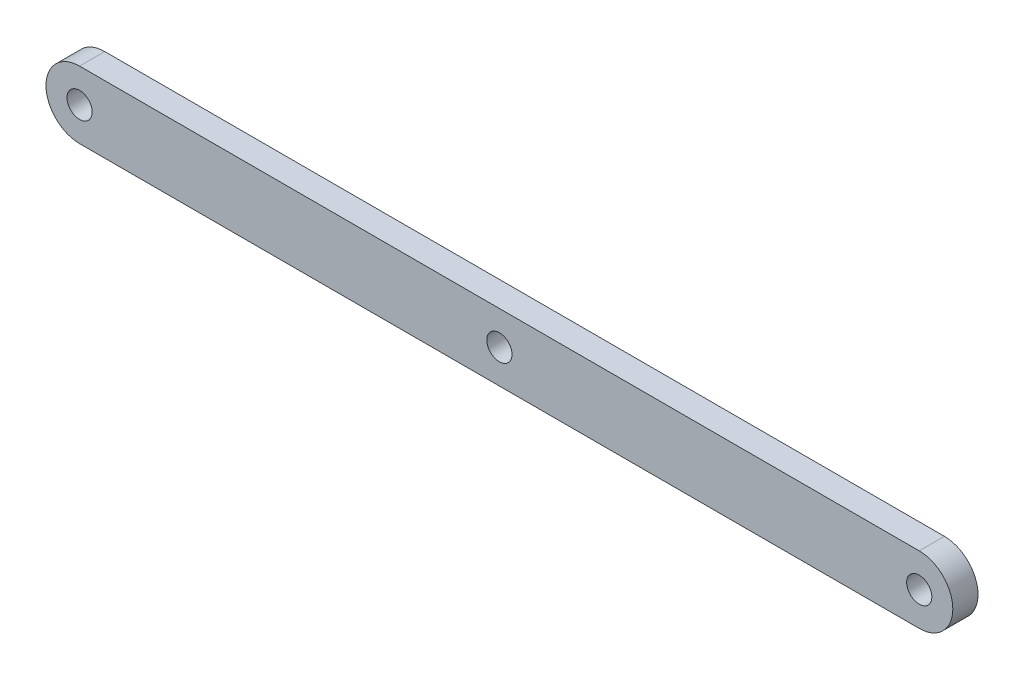
SolidWorks part; units mm, degrees
ref_plane "Front Plane" through (0, 0, 0) normal (0, 0, 1) x (1, 0, 0)
ref_plane "Top Plane" through (0, 0, 0) normal (0, 1, 0) x (1, 0, 0)
ref_plane "Right Plane" through (0, 0, 0) normal (1, 0, 0) x (0, 0, -1)
sketch "Sketch1" plane through (0, 0, 0) normal (0, 0, 1) x (1, 0, 0)
  line L0 (0, 4) -> (0, -4) construction
  line L3 (50, -4) -> (-50, -4)
  line L5 (50, 4) -> (-50, 4)
  line L6 (-50, -4) -> (-50, 4) construction
  line L7 (0, 0) -> (-50, 4) construction
  line L8 (0, 0) -> (-50, -4) construction
  line L9 (0, 0) -> (50, -4) construction
  line L10 (0, 0) -> (50, 4) construction
  line L11 (50, -4) -> (50, 4) construction
  arc A2 (-49.3641, 3.9491) -> (-49.3641, -3.9491) centre (-50, 0) ccw
  circle A3 centre (-50, 0) radius 1.5
  arc A4 (-49.3641, -3.9491) -> (-49.3641, 3.9491) centre (-50, 0) ccw construction
  arc A5 (49.3641, -3.9491) -> (49.3641, 3.9491) centre (50, 0) cw construction
  circle A6 centre (50, 0) radius 1.5
  arc A7 (49.3641, 3.9491) -> (49.3641, -3.9491) centre (50, 0) cw
  circle A8 centre (0, 0) radius 1.5
  point P0 (0, 0)
  dimension "D3" = 3
  dimension "D1" = 50
  dimension "D2" = 8
extrude "Boss-Extrude1" add sketch "Sketch1" along normal blind 3
